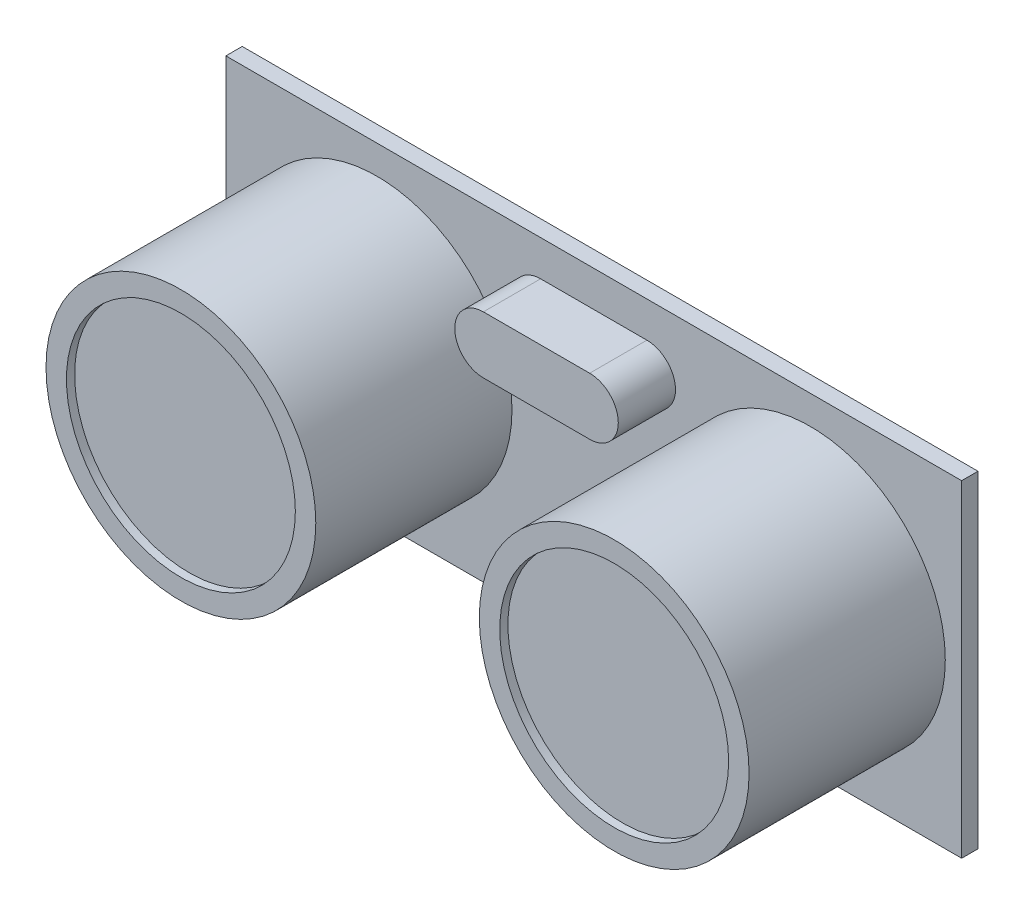
SolidWorks part; units mm, degrees
ref_plane "Plano frontal" through (0, 0, 0) normal (0, 0, 1) x (1, 0, 0)
ref_plane "Plano superior" through (0, 0, 0) normal (0, 1, 0) x (1, 0, 0)
ref_plane "Plano direito" through (0, 0, 0) normal (1, 0, 0) x (0, 0, -1)
sketch "Esboço1" plane through (0, 0, 0) normal (0, 0, 1) x (1, 0, 0)
  line L1 (0, 0) -> (45, 0)
  line L2 (0, 0) -> (0, 20)
  line L3 (0, 20) -> (45, 20)
  line L4 (45, 0) -> (45, 20)
  dimension "D1" = 45
  dimension "D2" = 20
extrude "Ressalto-extrusão1" add sketch "Esboço1" along normal blind 1
sketch "Esboço2" plane through (0, 0, 1) normal (0, 0, 1) x (1, 0, 0)
  line L0 (0, 10) -> (45, 10) construction
  line L1 (0, 20) -> (0, 0) construction
  line L2 (45, 0) -> (45, 20) construction
  line L3 (9.25, 20) -> (9.25, 0) construction
  line L4 (45, 20) -> (0, 20) construction
  line L5 (0, 0) -> (45, 0) construction
  line L6 (35.75, 20) -> (35.75, 0) construction
  circle A0 centre (9.25, 10) radius 8.25
  circle A1 centre (35.75, 10) radius 8.25
  dimension "D1" = 26.5
  dimension "D2" = 9.25
extrude "Ressalto-extrusão2" add sketch "Esboço2" along normal blind 12
sketch "Esboço3" plane through (0, 0, 13) normal (0, 0, 1) x (1, 0, 0)
  circle A0 centre (9.25, 10) radius 7
  circle A1 centre (35.75, 10) radius 7
extrude "Corte-extrusão1" cut sketch "Esboço3" against normal blind 0.5
sketch "Esboço6" plane through (0, 0, 1) normal (0, 0, 1) x (1, 0, 0)
  line L0 (22.5, 20) -> (22.5, 0) construction
  line L1 (17.5, 14.3168) -> (27.5, 14.3168)
  line L2 (17.5, 14.3168) -> (17.5, 17.8168)
  line L3 (17.5, 17.8168) -> (27.5, 17.8168)
  line L4 (27.5, 14.3168) -> (27.5, 17.8168)
  line L5 (45, 20) -> (0, 20) construction
  line L6 (0, 0) -> (45, 0) construction
  circle A2 centre (19.25, 16.0668) radius 1.75
  circle A3 centre (25.75, 16.0668) radius 1.75
  dimension "D1" = 10
  dimension "D2" = 3.5
  dimension "D3" = 5
extrude "Ressalto-extrusão5" add sketch "Esboço6" along normal blind 3.5 contours A2 | L0 L3 A2 L1 | L3 L0 L1 A3 | A3
sketch "Esboço7" plane through (0, 0, 0) normal (0, 0, -1) x (-1, 0, 0)
  line L0 (0, 0) -> (-45, 0) construction
  line L1 (-27.5, 0) -> (-17.5, 0)
  line L2 (-27.5, 0) -> (-27.5, 2)
  line L3 (-27.5, 2) -> (-17.5, 2)
  line L4 (-17.5, 0) -> (-17.5, 2)
  line L5 (-22.5, 20) -> (-22.5, 0) construction
  line L6 (-25.5, 2) -> (-25.5, 0)
  line L7 (-45, 20) -> (0, 20) construction
  line L8 (-23.5, 2) -> (-23.5, 0)
  line L9 (-21.5, 2) -> (-21.5, 0)
  line L10 (-19.5, 2) -> (-19.5, 0)
  line L11 (-25.6, 2) -> (-25.6, 0)
  line L12 (-23.6, 2) -> (-23.6, 0)
  line L13 (-21.6, 2) -> (-21.6, 0)
  line L14 (-19.6, 2) -> (-19.6, 0)
  line L15 (-27.6, -0.1) -> (-27.6, 2.1)
  line L16 (-27.6, 2.1) -> (-17.4, 2.1)
  line L17 (-17.4, -0.1) -> (-17.4, 2.1)
  line L18 (-27.6, -0.1) -> (-17.4, -0.1)
  line L19 (-25.4, 2) -> (-25.4, 0)
  line L20 (-23.4, 2) -> (-23.4, 0)
  line L21 (-21.4, 2) -> (-21.4, 0)
  line L22 (-19.4, 2) -> (-19.4, 0)
  line L23 (-27.4, 0.1) -> (-27.4, 1.9)
  line L24 (-27.4, 1.9) -> (-17.6, 1.9)
  line L25 (-17.6, 0.1) -> (-17.6, 1.9)
  line L26 (-27.4, 0.1) -> (-17.6, 0.1)
  line L28 (-25.6, 1.9) -> (-19.4, 1.9)
  line L29 (-25.6, 1.9) -> (-25.6, 0.1)
  line L30 (-25.6, 0.1) -> (-19.4, 0.1)
  line L31 (-19.4, 1.9) -> (-19.4, 0.1)
  line M23 (-45, 0) -> (0, 0)
  dimension "D1" = 5
  dimension "D2" = 10
  dimension "D3" = 2
  dimension "D4" = 2
  dimension "D5" = 2
  dimension "D6" = 2
  dimension "D7" = 2
  dimension "D10" = 0.1
  dimension "D11" = 0.1
  dimension "D8" = 0.1
  dimension "D9" = 0.1
extrude "Ressalto-extrusão6" add sketch "Esboço7" along normal blind 2 contours L23 L26 L11 L24 | L19 L26 L12 L24 | L5 L24 L20 L26 | L28 L5 L30 L13 | L21 L26 L14 L24 | L22 L26 L25 L24 | L26 L23 L24 L11 L3 L2 M23 | L19 L24 L12 L3 | L5 L3 L20 L24 | L3 L5 L28 L13 | L21 L24 L14 L3 | L26 L22 L1 L4 L3 L24 L25 | L26 L19 L12 M23 | L5 L26 L20 L1 | L30 L5 L13 M23 | L26 L21 L14 M23
sketch "Esboço9" plane through (0, 0, -2) normal (0, 0, -1) x (-1, 0, 0)
  line L0 (-17.5, 0) -> (-17.5, 2) construction
  line L1 (-27.5, 0) -> (-17.5, 0)
  line L2 (-27.5, 0) -> (-27.5, 0.1)
  line L3 (-27.5, 0.1) -> (-17.5, 0.1)
  line L4 (-17.5, 0) -> (-17.5, 0.1)
  dimension "D1" = 0.1
extrude "Corte-extrusão2" cut sketch "Esboço9" against normal blind 2
sketch "Esboço10" plane through (0, 0, -2) normal (0, 0, -1) x (-1, 0, 0)
  line L0 (-27.5, 1.05) -> (-25, 1.05) construction
  line L1 (-27.5, 0.1) -> (-27.5, 2) construction
  line L2 (-17.5, 0.1) -> (-17.5, 2) construction
  line L3 (-26.55, 2) -> (-26.55, 0.1) construction
  line L4 (-27.5, 2) -> (-25.6, 2) construction
  line L5 (-25.6, 0.1) -> (-27.5, 0.1) construction
  line L6 (-24.5, 2) -> (-24.5, 1.55) construction
  line L7 (-25.4, 2) -> (-23.6, 2) construction
  line L8 (-23.6, 0.1) -> (-25.4, 0.1) construction
  line L9 (-22.5, 2) -> (-22.5, 0.1) construction
  line L10 (-23.4, 2) -> (-21.6, 2) construction
  line L11 (-21.6, 0.1) -> (-23.4, 0.1) construction
  line L12 (-20.5, 2) -> (-20.5, 0.1) construction
  line L13 (-21.4, 2) -> (-19.6, 2) construction
  line L14 (-19.6, 0.1) -> (-21.4, 0.1) construction
  line L15 (-18.45, 2) -> (-18.45, 0.1) construction
  line L16 (-19.4, 2) -> (-17.5, 2) construction
  line L17 (-17.5, 0.1) -> (-19.4, 0.1) construction
  line L18 (-25, 0.55) -> (-24, 0.55)
  line L21 (-25, 1.55) -> (-24, 1.55)
  line L22 (-24, 0.55) -> (-24, 1.55)
  line L23 (-25, 0.55) -> (-25, 1.55)
  line L24 (-24.5, 0.55) -> (-24.5, 0.1) construction
  line L25 (-24, 1.05) -> (-17.5, 1.05) construction
  line L26 (-27.05, 0.55) -> (-26.05, 0.55)
  line L27 (-27.05, 1.55) -> (-26.05, 1.55)
  line L28 (-26.05, 0.55) -> (-26.05, 1.55)
  line L29 (-27.05, 0.55) -> (-27.05, 1.55)
  line L30 (-22.9724, 0.55) -> (-21.9724, 0.55)
  line L31 (-22.9724, 1.55) -> (-21.9724, 1.55)
  line L32 (-21.9724, 0.55) -> (-21.9724, 1.55)
  line L33 (-22.9724, 0.55) -> (-22.9724, 1.55)
  line L34 (-20.9694, 0.55) -> (-19.9694, 0.55)
  line L35 (-20.9694, 1.55) -> (-19.9694, 1.55)
  line L36 (-19.9694, 0.55) -> (-19.9694, 1.55)
  line L37 (-20.9694, 0.55) -> (-20.9694, 1.55)
  line L38 (-18.9714, 0.55) -> (-17.9714, 0.55)
  line L39 (-18.9714, 1.55) -> (-17.9714, 1.55)
  line L40 (-17.9714, 0.55) -> (-17.9714, 1.55)
  line L41 (-18.9714, 0.55) -> (-18.9714, 1.55)
  dimension "D1" = 0.5
  dimension "D2" = 0.5
  dimension "D3" = 0.5
  dimension "D4" = 1
  dimension "D5" = 1
  dimension "D6" = 1
  dimension "D7" = 1
  dimension "D8" = 1
  dimension "D9" = 1
  dimension "D10" = 1
  dimension "D11" = 1
  dimension "D12" = 1
  dimension "D13" = 1
  dimension "D14" = 0.5
  dimension "D15" = 0.5
  dimension "D16" = 0.5
  dimension "D17" = 0.5
  dimension "D18" = 0.5
extrude "Ressalto-extrusão7" add sketch "Esboço10" along normal blind 2
sketch "Esboço11" plane through (0, 0.55, 0) normal (0, -1, 0) x (1, 0, 0)
  line L0 (26.05, -4) -> (26.05, -2) construction
  line L1 (27.05, -4) -> (26.05, -4)
  line L2 (27.05, -4) -> (27.05, -3)
  line L3 (27.05, -3) -> (26.05, -3)
  line L4 (26.05, -4) -> (26.05, -3)
  line L21 (24, -4) -> (24, -2) construction
  line L22 (25, -4) -> (24, -4)
  line L23 (25, -4) -> (25, -3)
  line L24 (25, -3) -> (24, -3)
  line L25 (24, -4) -> (24, -3)
  line L26 (22.9724, -4) -> (22.9724, -2) construction
  line L27 (22.9724, -4) -> (21.9724, -4)
  line L28 (22.9724, -4) -> (22.9724, -3.0323)
  line L29 (22.9724, -3.0323) -> (21.9724, -3.0323)
  line L30 (21.9724, -4) -> (21.9724, -3.0323)
  line L31 (21.9724, -4) -> (21.9724, -2) construction
  line L32 (19.9694, -4) -> (19.9694, -2) construction
  line L33 (20.9694, -4) -> (19.9694, -4)
  line L34 (20.9694, -4) -> (20.9694, -3.0323)
  line L35 (20.9694, -3.0323) -> (19.9694, -3.0323)
  line L36 (19.9694, -4) -> (19.9694, -3.0323)
  line L37 (17.9714, -4) -> (17.9714, -2) construction
  line L38 (18.9714, -4) -> (17.9714, -4)
  line L39 (18.9714, -4) -> (18.9714, -3.0323)
  line L40 (18.9714, -3.0323) -> (17.9714, -3.0323)
  line L41 (17.9714, -4) -> (17.9714, -3.0323)
  dimension "D1" = 1
extrude "Ressalto-extrusão8" add sketch "Esboço11" along normal blind 4
